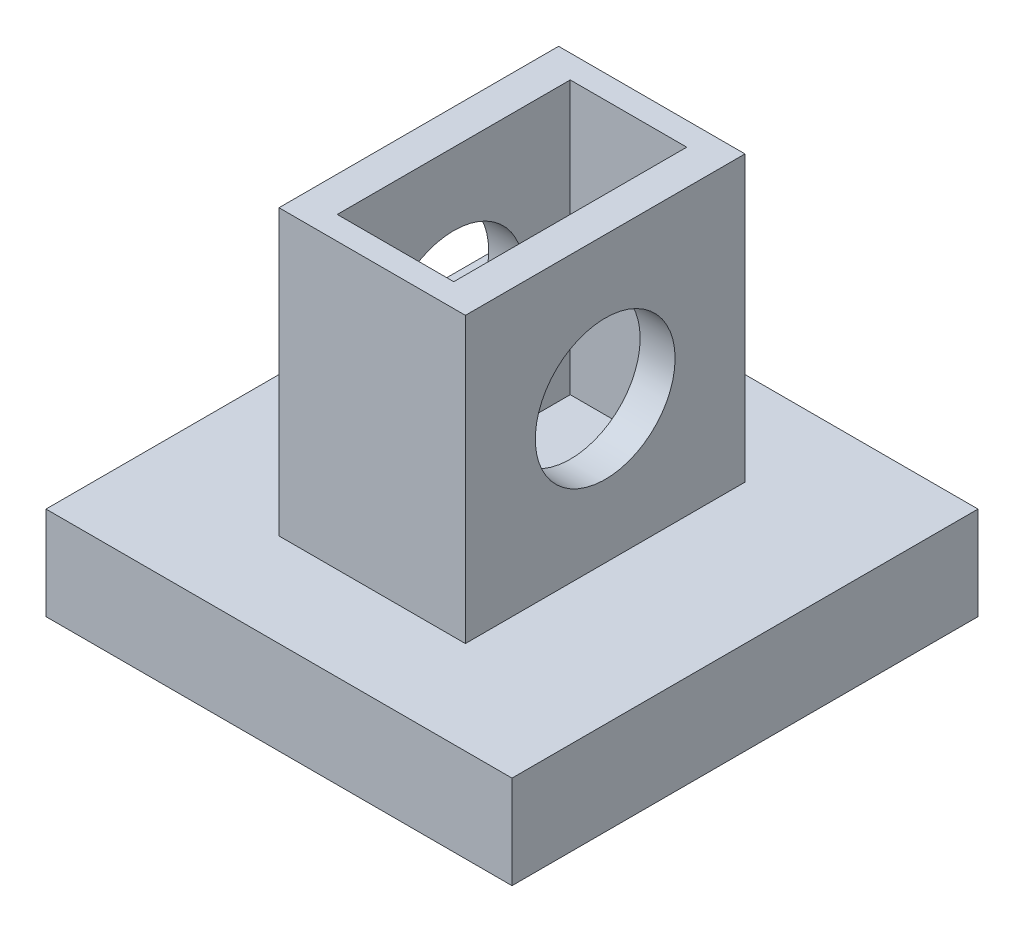
SolidWorks part; units mm, degrees
ref_plane "Front Plane" through (0, 0, 0) normal (0, 0, 1) x (1, 0, 0)
ref_plane "Top Plane" through (0, 0, 0) normal (0, 1, 0) x (1, 0, 0)
ref_plane "Right Plane" through (0, 0, 0) normal (1, 0, 0) x (0, 0, -1)
sketch "Sketch2" plane through (0, 0, 0) normal (0, 1, 0) x (1, 0, 0)
  line L1 (-40.4037, -4.3322) -> (1.5963, -4.3322)
  line L2 (-40.4037, -4.3322) -> (-40.4037, -20.3322)
  line L3 (-40.4037, -20.3322) -> (1.5963, -20.3322)
  line L4 (1.5963, -4.3322) -> (1.5963, -20.3322)
extrude "Boss-Extrude1" add sketch "Sketch2" along normal blind 4
sketch "Sketch9" plane through (0, 4, 0) normal (0, 1, 0) x (1, 0, 0)
  line L1 (-40.4037, -20.3322) -> (1.5963, -20.3322) construction
  line L5 (-23.4037, -20.3322) -> (-15.4037, -20.3322)
  line L6 (-23.4037, -20.3322) -> (-23.4037, -8.3322)
  line L7 (-23.4037, -8.3322) -> (-15.4037, -8.3322)
  line L8 (-15.4037, -20.3322) -> (-15.4037, -8.3322)
extrude "Boss-Extrude3" add sketch "Sketch9" along normal blind 12.2
sketch "Sketch10" plane through (0, 16.2, 0) normal (0, 1, 0) x (1, 0, 0)
  line L10 (-21.9037, -9.3322) -> (-16.9037, -9.3322)
  line L11 (-21.9037, -9.3322) -> (-21.9037, -19.3322)
  line L12 (-21.9037, -19.3322) -> (-16.9037, -19.3322)
  line L13 (-16.9037, -9.3322) -> (-16.9037, -19.3322)
extrude "Cut-Extrude6" cut sketch "Sketch10" against normal blind 11.7
sketch "Sketch12" plane through (-15.4037, 0, 0) normal (1, 0, 0) x (0, 0, -1)
  circle A0 centre (-14.3322, 10.1) radius 3
extrude "Cut-Extrude7" cut sketch "Sketch12" against normal blind 8
sketch "Sketch17" plane through (0, 0, 20.3322) normal (0, 0, 1) x (1, 0, 0)
  line L1 (-40.4037, 0) -> (1.5963, 0)
  line L2 (-40.4037, 0) -> (-40.4037, 4)
  line L3 (-40.4037, 4) -> (1.5963, 4)
  line L4 (1.5963, 0) -> (1.5963, 4)
extrude "Boss-Extrude4" add sketch "Sketch17" along normal blind 4
sketch "Sketch21" plane through (-40.4037, 0, 0) normal (-1, 0, 0) x (0, 0, 1)
  line L1 (4.3322, 0) -> (24.3322, 0)
  line L2 (4.3322, 0) -> (4.3322, 4)
  line L3 (4.3322, 4) -> (24.3322, 4)
  line L4 (24.3322, 0) -> (24.3322, 4)
extrude "Cut-Extrude8" cut sketch "Sketch21" against normal blind 11
sketch "Sketch22" plane through (1.5963, 0, 0) normal (1, 0, 0) x (0, 0, -1)
  line L1 (-4.3322, 4) -> (-24.3322, 4)
  line L2 (-4.3322, 4) -> (-4.3322, 0)
  line L3 (-4.3322, 0) -> (-24.3322, 0)
  line L4 (-24.3322, 4) -> (-24.3322, 0)
extrude "Cut-Extrude9" cut sketch "Sketch22" against normal blind 11
